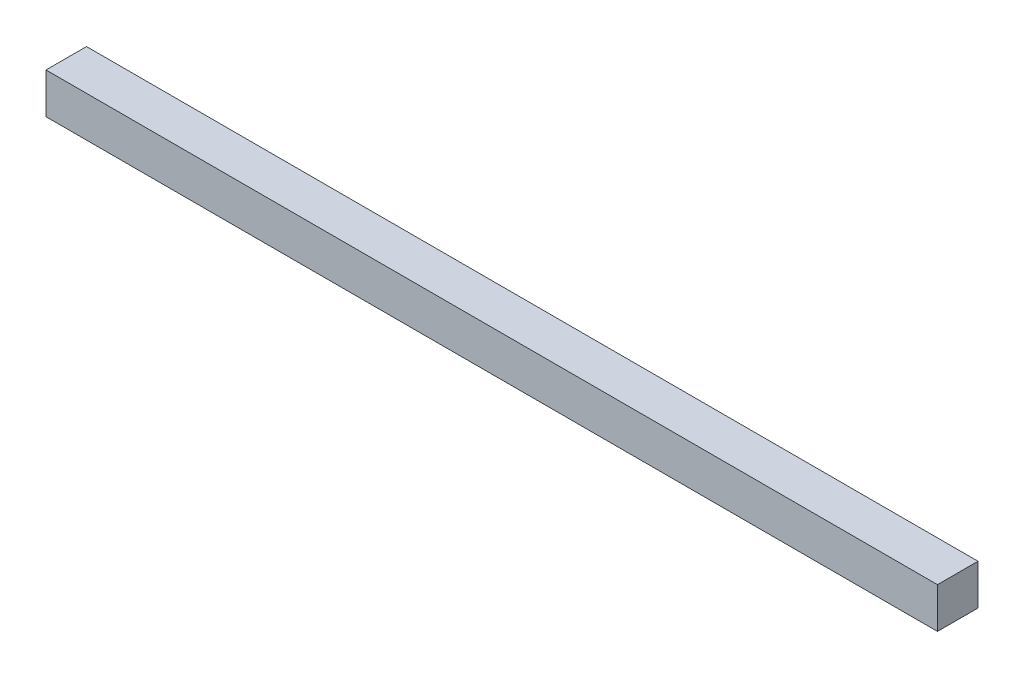
SolidWorks part; units mm, degrees
ref_plane "Plan de face" through (0, 0, 0) normal (0, 0, 1) x (1, 0, 0)
ref_plane "Plan de dessus" through (0, 0, 0) normal (0, 1, 0) x (1, 0, 0)
ref_plane "Plan de droite" through (0, 0, 0) normal (1, 0, 0) x (0, 0, -1)
sketch "Esquisse1" plane through (0, 0, 0) normal (0, 0, 1) x (1, 0, 0)
  line L1 (-5500, -250) -> (5500, -250)
  line L2 (-5500, -250) -> (-5500, 250)
  line L3 (-5500, 250) -> (5500, 250)
  line L4 (5500, -250) -> (5500, 250)
  line L5 (-5500, -250) -> (5500, 250) construction
  line L6 (-5500, 250) -> (5500, -250) construction
  point P0 (0, 0)
  dimension "D1" = 11000
  dimension "D2" = 500
extrude "Boss.-Extru.1" add sketch "Esquisse1" along normal blind 500
